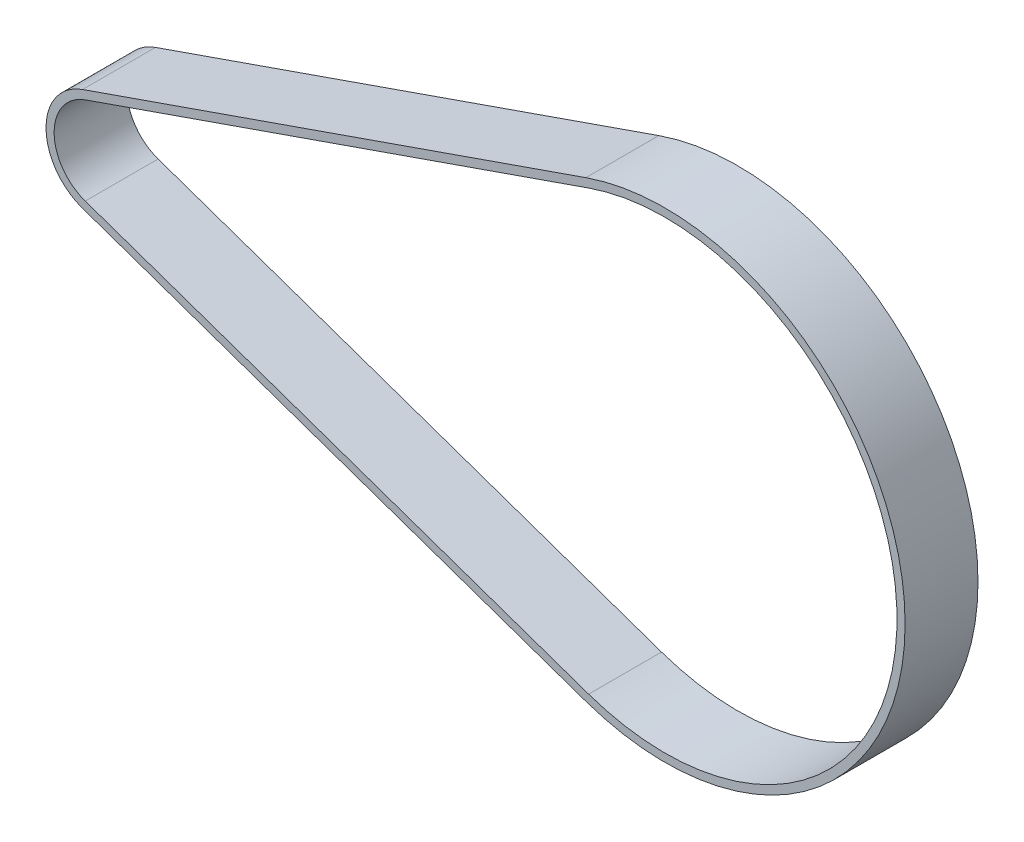
SolidWorks part; units mm, degrees
material "SBR"
ref_plane "Front Plane" through (0, 0, 0) normal (0, 0, 1) x (1, 0, 0)
ref_plane "Top Plane" through (0, 0, 0) normal (0, 1, 0) x (1, 0, 0)
ref_plane "Right Plane" through (0, 0, 0) normal (1, 0, 0) x (0, 0, -1)
sketch "Sketch1" plane through (0, 0, 0) normal (0, 0, 1) x (1, 0, 0)
  line L0 (-36.7296, 5.4108) -> (25.4214, 27.0571) construction
  line L1 (25.4214, -27.0571) -> (-36.7296, -5.4108) construction
  line L2 (-34.8451, 0) -> (34.8451, 0) construction
  line L3 (25.0925, -28.0015) -> (-37.0585, -6.3552)
  line L4 (-37.0585, 6.3552) -> (25.0925, 28.0015)
  line L5 (25.4214, -27.0571) -> (-36.7296, -5.4108)
  line L6 (-36.7296, 5.4108) -> (25.4214, 27.0571)
  arc A0 (-36.7296, 5.4108) -> (-36.7296, -5.4108) centre (-34.8451, 0) ccw construction
  arc A1 (25.4214, -27.0571) -> (25.4214, 27.0571) centre (34.8451, 0) ccw construction
  arc A2 (-37.0585, 6.3552) -> (-37.0585, -6.3552) centre (-34.8451, 0) ccw
  arc A3 (25.0925, -28.0015) -> (25.0925, 28.0015) centre (34.8451, 0) ccw
  arc A4 (-36.7296, 5.4108) -> (-36.7296, -5.4108) centre (-34.8451, 0) ccw
  arc A5 (25.4214, -27.0571) -> (25.4214, 27.0571) centre (34.8451, 0) ccw
  point P3 (0, 0)
  dimension "D1" = 57.3024
  dimension "D2" = 11.4592
  dimension "D3" = 69.6901
  dimension "D4" = 255
  dimension "D5" = 1
  dimension "D6" = 0
extrude "Boss-Extrude2" add sketch "Sketch1" along normal blind 9
